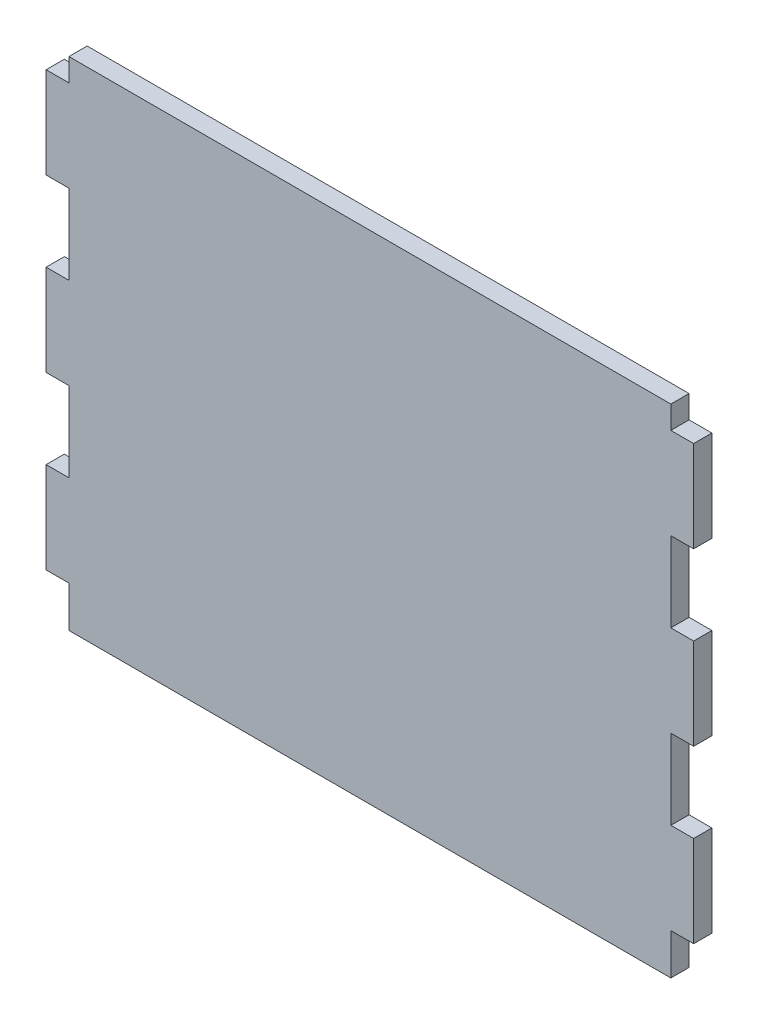
SolidWorks part; units mm, degrees
ref_plane "Front Plane" through (0, 0, 0) normal (0, 0, 1) x (1, 0, 0)
ref_plane "Top Plane" through (0, 0, 0) normal (0, 1, 0) x (1, 0, 0)
ref_plane "Right Plane" through (0, 0, 0) normal (1, 0, 0) x (0, 0, -1)
sketch "Sketch1" plane through (0, 0, 0) normal (0, 0, 1) x (1, 0, 0)
  line L0 (-90.17, 0) -> (0, 0) construction
  line L1 (83.82, -69.215) -> (-83.82, -69.215)
  line L2 (83.82, -69.215) -> (83.82, -57.785)
  line L3 (83.82, 69.215) -> (-83.82, 69.215)
  line L4 (-83.82, -69.215) -> (-83.82, -57.785)
  line L5 (83.82, -69.215) -> (-83.82, 69.215) construction
  line L6 (83.82, 69.215) -> (-83.82, -69.215) construction
  line L7 (-90.17, 37.465) -> (-90.17, 15.24) construction
  line L8 (-83.82, 15.24) -> (-90.17, 15.24)
  line L10 (-83.82, -10.16) -> (-90.17, -10.16)
  line L11 (-90.17, 15.24) -> (-90.17, -10.16)
  line L12 (-83.82, 62.865) -> (-90.17, 62.865)
  line L14 (-83.82, 37.465) -> (-90.17, 37.465)
  line L15 (-90.17, 62.865) -> (-90.17, 37.465)
  line L16 (-83.82, -32.385) -> (-90.17, -32.385)
  line L18 (-83.82, -57.785) -> (-90.17, -57.785)
  line L19 (-90.17, -32.385) -> (-90.17, -57.785)
  line L20 (-90.17, -10.16) -> (-90.17, -32.385) construction
  line L21 (0, 69.215) -> (0, -69.215) construction
  line L22 (-83.82, 62.865) -> (-83.82, 69.215)
  line L23 (-83.82, 15.24) -> (-83.82, 37.465)
  line L24 (-83.82, -32.385) -> (-83.82, -10.16)
  line L25 (83.82, 62.865) -> (90.17, 62.865)
  line L26 (83.82, 15.24) -> (90.17, 15.24)
  line L27 (83.82, 37.465) -> (90.17, 37.465)
  line L28 (83.82, -10.16) -> (90.17, -10.16)
  line L29 (83.82, -32.385) -> (90.17, -32.385)
  line L30 (83.82, -57.785) -> (90.17, -57.785)
  line L31 (90.17, -10.16) -> (90.17, -32.385) construction
  line L32 (90.17, 37.465) -> (90.17, 15.24) construction
  line L33 (90.17, -32.385) -> (90.17, -57.785)
  line L34 (90.17, 62.865) -> (90.17, 37.465)
  line L35 (90.17, 15.24) -> (90.17, -10.16)
  line L36 (83.82, 62.865) -> (83.82, 69.215)
  line L37 (83.82, 15.24) -> (83.82, 37.465)
  line L38 (83.82, -32.385) -> (83.82, -10.16)
  point P0 (0, 0)
  point P12 (-90.17, 11.9328)
  dimension "D1" = 167.64
  dimension "D2" = 138.43
  dimension "D3" = 25.4
  dimension "D4" = 6.35
  dimension "D5" = 6.35
  dimension "D6" = 15.24
extrude "Boss-Extrude1" add sketch "Sketch1" along normal blind 5.08
